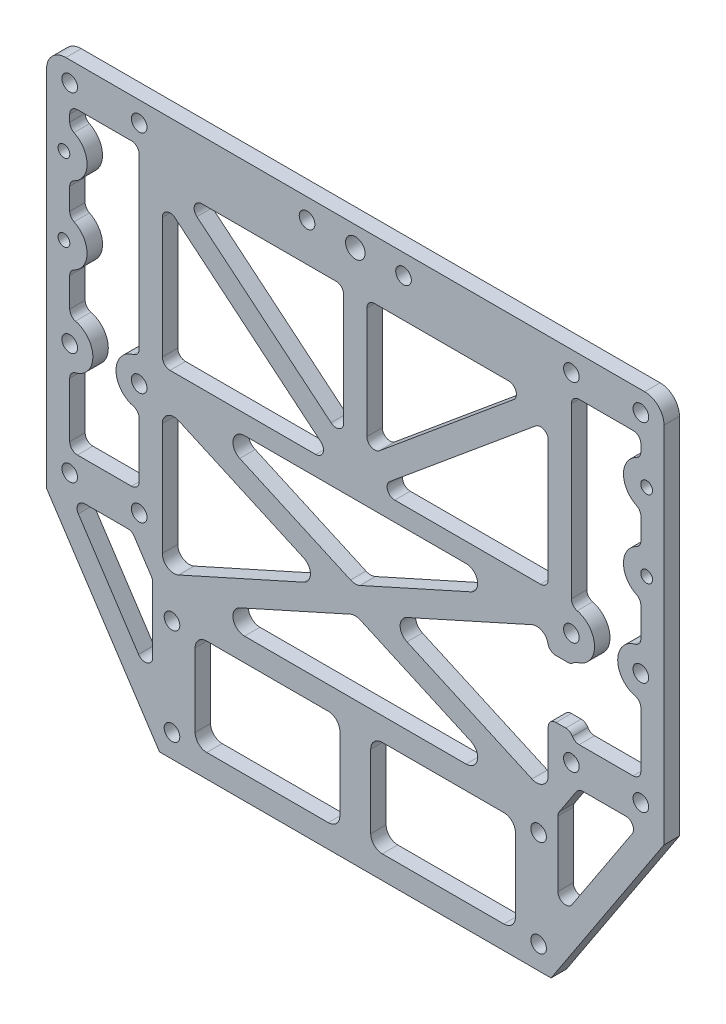
SolidWorks part; units mm, degrees
material "Thornel Mat VMA"
ref_plane "前视基准面" through (0, 0, 0) normal (0, 0, 1) x (1, 0, 0)
ref_plane "上视基准面" through (0, 0, 0) normal (0, 1, 0) x (1, 0, 0)
ref_plane "右视基准面" through (0, 0, 0) normal (1, 0, 0) x (0, 0, -1)
other "Configuration Table"
sketch "草图1" plane through (0, 0, 0) normal (0, 0, 1) x (1, 0, 0)
  line L0 (0, 0) -> (0, -50000) construction
  line L1 (-74, -14.5) -> (74, -14.5) construction
  line L2 (-74, -14.5) -> (-74, 14.5) construction
  line L3 (-74, 14.5) -> (74, 14.5) construction
  line L4 (74, -14.5) -> (74, 14.5) construction
  line L5 (-74, -14.5) -> (74, 14.5) construction
  line L6 (-74, 14.5) -> (74, -14.5) construction
  line L7 (-80, -14.5) -> (80, -14.5) construction
  line L8 (-80, -14.5) -> (-80, 14.5) construction
  line L9 (-80, 14.5) -> (80, 14.5) construction
  line L10 (80, -14.5) -> (80, 14.5) construction
  line L11 (-80, -14.5) -> (80, 14.5) construction
  line L12 (-80, 14.5) -> (80, -14.5) construction
  line L13 (-74, 14.5) -> (74, 14.5) construction
  line L14 (-74, 14.5) -> (-74, 73) construction
  line L15 (-74, 73) -> (74, 73) construction
  line L16 (74, 14.5) -> (74, 73) construction
  line L17 (-80, -14.5) -> (80, -14.5)
  line L18 (-80, -14.5) -> (-80, -21)
  line L19 (-80, -21) -> (80, -21)
  line L20 (80, -14.5) -> (80, -21)
  line L21 (-80, -21) -> (-50.7354, -65.5)
  line L22 (-47.5, -59.5) -> (47.5, -59.5) construction
  line L23 (-47.5, -59.5) -> (-47.5, -34.5) construction
  line L24 (-47.5, -34.5) -> (47.5, -34.5) construction
  line L25 (47.5, -59.5) -> (47.5, -34.5) construction
  line L26 (-47.5, -59.5) -> (47.5, -34.5) construction
  line L27 (-47.5, -34.5) -> (47.5, -59.5) construction
  line L28 (-50.7354, -65.5) -> (50.7354, -65.5)
  line L29 (50.7354, -65.5) -> (80, -21)
  line L31 (-80, -14.5) -> (80, -14.5)
  line L32 (-80, -14.5) -> (-80, 83)
  line L33 (-80, 83) -> (80, 83)
  line L34 (80, -14.5) -> (80, 83)
  circle A0 centre (-74, 14.5) radius 2.025
  circle A1 centre (-74, -14.5) radius 2.025
  circle A2 centre (74, -14.5) radius 2.025
  circle A3 centre (74, 14.5) radius 2.025
  circle A4 centre (-74, 73) radius 2.025
  circle A5 centre (74, 73) radius 2.025
  circle A6 centre (-47.5, -34.5) radius 2.025
  circle A7 centre (-47.5, -59.5) radius 2.025
  circle A8 centre (47.5, -34.5) radius 2.025
  circle A9 centre (47.5, -59.5) radius 2.025
  circle A10 centre (-47.5, -59.5) radius 6 construction
  circle A11 centre (74, 73) radius 6 construction
  point P0 (0, 0)
  point P6 (0, 0)
  point P22 (0, -47)
  dimension "D3" = 4.05
  dimension "D1" = 148
  dimension "D2" = 160
  dimension "D4" = 29
  dimension "D5" = 87.5
  dimension "D6" = 6.5
  dimension "D7" = 25
  dimension "D8" = 95
  dimension "D9" = 6
  dimension "D10" = 26
  dimension "D11" = 10
extrude "凸台-拉伸1" add sketch "草图1" along normal blind 4 contours A2 L17 L34 L33 L32 A1 A5 A4 A3 A0 | A2 L17 A1 L18 L19 L20 | L28 L29 L19 L21 A9 A8 A7 A6
sketch "草图2" plane through (0, 0, 4) normal (0, 0, 1) x (1, 0, 0)
  line L0 (0, 0) -> (0, -50000) construction
  circle A0 centre (-74, -14.5) radius 2.025 construction
  circle A1 centre (-74, 14.5) radius 2.025 construction
  circle A2 centre (-74, 73) radius 2.025 construction
  circle A3 centre (-74, -14.5) radius 2.025
  circle A4 centre (-74, 14.5) radius 2.025
  circle A5 centre (-74, 73) radius 2.025
  circle A6 centre (-56, 73) radius 2.025
  circle A7 centre (-56, 14.5) radius 2.025
  circle A8 centre (-56, -14.5) radius 2.025
  circle A9 centre (56, -14.5) radius 2.025
  circle A10 centre (56, 14.5) radius 2.025
  circle A11 centre (56, 73) radius 2.025
  dimension "D2" = 18
  dimension "D1" = 2
extrude "切除-拉伸1" cut sketch "草图2" against normal blind 10
sketch "草图3" plane through (0, 0, 4) normal (0, 0, 1) x (1, 0, 0)
  line L0 (-56, 73) -> (56, 73) construction
  circle A0 centre (0, 73) radius 2.525
  dimension "D1" = 5.05
extrude "切除-拉伸2" cut sketch "草图3" against normal blind 10
sketch "草图4" plane through (0, 0, 4) normal (0, 0, 1) x (1, 0, 0)
  line L0 (-80, -21) -> (-80, 83) construction
  line L1 (0, 0) -> (0, -50000) construction
  line L2 (-47.5, -34.5) -> (-47.5, -59.5) construction
  line L3 (-41.5, -59.5) -> (-4, -59.5)
  line L4 (-41.5, -59.5) -> (-41.5, -34.5)
  line L5 (-41.5, -34.5) -> (-4, -34.5)
  line L6 (-4, -59.5) -> (-4, -34.5)
  line L7 (-41.5, -59.5) -> (-4, -34.5) construction
  line L8 (-41.5, -34.5) -> (-4, -59.5) construction
  line L9 (4, -59.5) -> (41.5, -59.5)
  line L10 (4, -59.5) -> (4, -34.5)
  line L11 (4, -34.5) -> (41.5, -34.5)
  line L12 (41.5, -59.5) -> (41.5, -34.5)
  line L13 (4, -59.5) -> (41.5, -34.5) construction
  line L14 (4, -34.5) -> (41.5, -59.5) construction
  line L15 (-47.5, -47) -> (-50047.5, -47) construction
  line L16 (-50.7354, -65.5) -> (50.7354, -65.5) construction
  line L17 (-74.4629, -18.5) -> (-36.5763, -18.5) construction
  line L18 (-36.5763, -18.5) -> (-30, -28.5) construction
  line L19 (-30, -28.5) -> (-67.8866, -28.5) construction
  line L20 (-67.8866, -28.5) -> (-74.4629, -18.5) construction
  line L21 (-80, -21) -> (-50.7354, -65.5) construction
  line L22 (80, -21) -> (80, 83) construction
  line L23 (-80, 20.5) -> (80, 20.5) construction
  line L24 (-80, 20.5) -> (-80, -18.5) construction
  line L25 (-80, -18.5) -> (80, -18.5) construction
  line L26 (80, 20.5) -> (80, -18.5) construction
  line L27 (-48.7689, -31.2358) -> (51.2311, 13.7642)
  line L28 (-50, -28.5) -> (50, -28.5)
  line L29 (-50, -28.5) -> (-50, 16.5)
  line L30 (-50, 16.5) -> (50, 16.5)
  line L31 (50, -28.5) -> (50, 16.5)
  line L32 (-50, -28.5) -> (50, 16.5) construction
  line L33 (-50, 16.5) -> (50, -28.5) construction
  line L34 (-51.2311, 13.7642) -> (48.7689, -31.2358)
  line L35 (-51.2311, -25.7642) -> (48.7689, 19.2358)
  line L36 (-48.7689, 19.2358) -> (51.2311, -25.7642)
  circle A0 centre (-74, 14.5) radius 6
  circle A1 centre (-56, 14.5) radius 6
  circle A3 centre (-56, -14.5) radius 2.025 construction
  point P11 (-22.75, -47)
  point P16 (22.75, -47)
  point P27 (-47.5, -47)
  point P44 (0, -6)
  dimension "D1" = 8
  dimension "D2" = 6
  dimension "D3" = 6
  dimension "D4" = 6
  dimension "D5" = 4
  dimension "D6" = 6
  dimension "D7" = 30
  dimension "D8" = 4
  dimension "D9" = 3
  dimension "D10" = 3
extrude "切除-拉伸3" cut sketch "草图4" against normal blind 10 contours L30 L36 L35 | L29 L35 L34 | L27 L36 L31 | L34 L27 L28 | L9 L12 L11 L10 | L3 L6 L5 L4
fillet "圆角2" radius 3 20 edges at (42.6894, -28.5, 2) (-42.6894, -28.5, 2) (0, -9.2898, 2) (-50, 13.2102, 2) (-7.3106, -6, 2) (-50, -25.2102, 2) (-41.5, -34.5, 2) (-4, -34.5, 2) (-4, -59.5, 2) (-41.5, -59.5, 2) (42.6894, 16.5, 2) (0, -2.7102, 2) (-42.6894, 16.5, 2) (50, 13.2102, 2) (50, -25.2102, 2) (7.3106, -6, 2) (4, -34.5, 2) (41.5, -34.5, 2) (4, -59.5, 2) (41.5, -59.5, 2)
sketch "草图5" plane through (0, 0, 4) normal (0, 0, 1) x (1, 0, 0)
  line L0 (-73.8053, -19.5) -> (-57.8852, -19.5)
  line L1 (-57.8852, -19.5) -> (-52.5, -27.6887)
  line L2 (-52.5, -27.6887) -> (-52.5, -51.897)
  line L3 (-52.5, -51.897) -> (-73.8053, -19.5)
  line L4 (-80, -21) -> (-50.7354, -65.5) construction
  line L5 (-47.5, -34.5) -> (-47.5, -59.5) construction
  line L6 (0, 0) -> (0, -50000) construction
  line L8 (52.5, -27.6887) -> (52.5, -51.897)
  line L9 (57.8852, -19.5) -> (52.5, -27.6887)
  line L10 (73.8053, -19.5) -> (57.8852, -19.5)
  line L11 (52.5, -51.897) -> (73.8053, -19.5)
  circle A0 centre (-74, -14.5) radius 2.025 construction
  point P7 (-65.3677, -43.25)
  dimension "D3" = 5
  dimension "D1" = 6
  dimension "D2" = 5
  dimension "D4" = 6
extrude "切除-拉伸4" cut sketch "草图5" against normal blind 10
sketch "草图6" plane through (0, 0, 4) normal (0, 0, 1) x (1, 0, 0)
  line L0 (80, -21) -> (80, 83) construction
  line L1 (-80, -21) -> (-80, 83) construction
  line L2 (-74, 68) -> (-56, 68)
  line L3 (-74, 68) -> (-74, -9.5)
  line L4 (-74, -9.5) -> (-56, -9.5)
  line L5 (-56, 68) -> (-56, -9.5)
  line L6 (-28.7122, 16.5) -> (28.7122, 16.5) construction
  line L7 (0, 0) -> (0, -50000) construction
  line L8 (74, -9.5) -> (56, -9.5)
  line L9 (56, 68) -> (56, -9.5)
  line L10 (74, 68) -> (56, 68)
  line L11 (74, 68) -> (74, -9.5)
  line L17 (-50, 21.5) -> (50, 21.5)
  line L18 (-50, 21.5) -> (-50, 63)
  line L19 (-50, 63) -> (50, 63)
  line L20 (50, 21.5) -> (50, 63)
  line L21 (-50, 21.5) -> (50, 63) construction
  line L22 (-50, 63) -> (50, 21.5) construction
  circle A0 centre (-74, 14.5) radius 6
  circle A1 centre (-56, 14.5) radius 6
  circle A2 centre (56, 14.5) radius 6
  circle A3 centre (74, 14.5) radius 6
  circle A4 centre (-74, -14.5) radius 2.025 construction
  circle A5 centre (-74, 73) radius 2.025 construction
  circle A7 centre (0, 73) radius 2.525 construction
  point P31 (0, 42.25)
  dimension "D5" = 10
  dimension "D1" = 6
  dimension "D2" = 5
  dimension "D3" = 5
  dimension "D4" = 5
  dimension "D6" = 6
extrude "切除-拉伸5" cut sketch "草图6" against normal blind 10 contours L17 L20 L19 L18 | A1 L5 L2 L3 A0 L4 | A3 L11 L10 L9 A2 L8
sketch "草图7" plane through (0, 0, 4) normal (0, 0, 1) x (1, 0, 0)
  line L0 (-80, -21) -> (-80, 83) construction
  line L1 (-80, 78.2) -> (80, 78.2)
  line L2 (-80, 78.2) -> (-80, 83)
  line L3 (-80, 83) -> (80, 83)
  line L4 (80, 78.2) -> (80, 83)
  line L5 (80, -21) -> (80, 83) construction
  line L6 (-80, 83) -> (80, 83) construction
  dimension "D1" = 4.8
extrude "切除-拉伸7" cut sketch "草图7" against normal blind 10
fillet "圆角5" radius 5 2 edges at (80, 78.2, 2) (-80, 78.2, 2)
sketch "草图11" plane through (0, 0, 4) normal (0, 0, 1) x (1, 0, 0)
  line L0 (-50, 63) -> (0, 21.5) construction
  line L1 (-50, 21.5) -> (50, 21.5) construction
  line L2 (0, 21.5) -> (50, 63) construction
  line L3 (0, 21.5) -> (0, 63) construction
  line L4 (-50, 63) -> (50, 63) construction
  line L5 (-51.916, 60.6916) -> (-1.916, 19.1916)
  line L6 (1.916, 19.1916) -> (51.916, 60.6916)
  line L7 (3, 21.5) -> (3, 63)
  line L8 (-48.084, 65.3084) -> (1.916, 23.8084)
  line L9 (-1.916, 23.8084) -> (48.084, 65.3084)
  line L10 (-3, 21.5) -> (-3, 63)
  line L12 (-50, 63) -> (50, 63)
  line L13 (-50, 63) -> (-50, 21.5)
  line L14 (-50, 21.5) -> (50, 21.5)
  line L15 (50, 63) -> (50, 21.5)
  dimension "D1" = 3
  dimension "D2" = 3
extrude "凸台-拉伸2" add sketch "草图11" against normal up to surface (4 mm away) up to face at (-65, 21.875, 0)
fillet "圆角6" radius 2 36 edges at (74, 8.5, 2) (74, 20.5, 2) (74, -9.5, 2) (56, -9.5, 2) (56, 20.5, 2) (56, 8.5, 2) (56, 68, 2) (74, 68, 2) (73.8053, -19.5, 2) (52.5, -51.897, 2) (52.5, -27.6887, 2) (57.8852, -19.5, 2) (-57.8852, -19.5, 2) (-52.5, -27.6887, 2) (-52.5, -51.897, 2) (-73.8053, -19.5, 2) (50, 59.1013, 2) (50, 21.5, 2) (4.6973, 21.5, 2) (-56, 8.5, 2) (-56, 20.5, 2) (-56, -9.5, 2) (-74, 20.5, 2) (-74, 8.5, 2) (-74, 68, 2) (-56, 68, 2) (-3, 27.8887, 2) (-45.3027, 63, 2) (-3, 63, 2) (3, 27.8887, 2) (3, 63, 2) (45.3027, 63, 2) (-50, 21.5, 2) (-50, 59.1013, 2) (-4.6973, 21.5, 2) (-74, -9.5, 2)
sketch "草图13" plane through (0, 0, 4) normal (0, 0, 1) x (1, 0, 0)
  line L0 (-12.5, 73) -> (12.5, 73) construction
  circle A0 centre (-12.5, 73) radius 2.025
  circle A1 centre (12.5, 73) radius 2.025
  point P4 (0, 73)
  dimension "D1" = 4.05
  dimension "D2" = 25
extrude "切除-拉伸8" cut sketch "草图13" against normal blind 10
sketch "草图14" plane through (0, 0, 4) normal (0, 0, 1) x (1, 0, 0)
  line L0 (74, 14.5) -> (75.5, 14.5) construction
  line L1 (75.5, 14.5) -> (75.5, 37) construction
  line L2 (80, -21) -> (80, 73.2) construction
  line L3 (75.5, 37) -> (75.5, 57) construction
  line L4 (0, 0) -> (0, -50000) construction
  line L5 (-75.5, 37) -> (-75.5, 57) construction
  line L6 (-75.5, 14.5) -> (-75.5, 37) construction
  circle A0 centre (75.5, 37) radius 1.525
  circle A1 centre (75.5, 57) radius 1.525
  circle A2 centre (-75.5, 57) radius 1.525
  circle A3 centre (-75.5, 37) radius 1.525
  dimension "D1" = 4.5
  dimension "D3" = 3.05
  dimension "D2" = 22.5
  dimension "D4" = 20
extrude "切除-拉伸9" cut sketch "草图14" against normal blind 10
fillet "圆角7" radius 5 8 edges at (74, 56.725, 2) (74, 57.275, 2) (74, 36.725, 2) (74, 37.275, 2) (-74, 37.275, 2) (-74, 36.725, 2) (-74, 57.275, 2) (-74, 56.725, 2)
sketch "草图15" plane through (0, 0, 0) normal (0, 0, -1) x (-1, 0, 0)
  line L0 (-50, -20.5705) -> (-50, 8.5705) construction
  line L1 (-50, -7.5) -> (-57, -7.5)
  line L2 (-50, -7.5) -> (-50, 7.5)
  line L3 (-50, 7.5) -> (-57, 7.5)
  line L4 (-57, -7.5) -> (-57, 7.5)
  line L7 (-36.5, 7.5) -> (-77.5, 7.5) construction
  dimension "D1" = 15
  dimension "D2" = 7
extrude "切除-拉伸10" cut sketch "草图15" against normal blind 10
fillet "圆角8" radius 2 4 edges at (56, -7.5, 2) (56.1443, 7.5, 2) (50, -7.5, 2) (50, 7.5, 2)
sketch "草图16" plane through (0, 0, 0) normal (0, 0, -1) x (-1, 0, 0)
  line L0 (-74, 51.4931) -> (-74, 42.5069) construction
  line L1 (-74, 66) -> (-74, 62.5069) construction
  line L2 (-74, 51.4931) -> (-74, 42.5069)
  line L3 (-74, 66) -> (-74, 62.5069)
  line L4 (-74, 31.4931) -> (-74, 22.246) construction
  line L5 (-74, 31.4931) -> (-74, 22.246)
  line L6 (0, 0) -> (0, -50000) construction
  line L7 (74, 31.4931) -> (74, 22.246)
  line L8 (74, 51.4931) -> (74, 42.5069)
  line L9 (74, 66) -> (74, 62.5069)
  circle A0 centre (-75.5, 37) radius 6
  circle A1 centre (-75.5, 57) radius 6
  circle A2 centre (75.5, 57) radius 6
  circle A3 centre (75.5, 37) radius 6
  circle A4 centre (-75.5, 57) radius 1.525
  circle A5 centre (-75.5, 37) radius 1.525
  circle A6 centre (75.5, 57) radius 1.525
  circle A7 centre (75.5, 37) radius 1.525
  arc A8 (-72.5, 8.6905) -> (-72.5, 20.3095) centre (-74, 14.5) ccw construction
  arc A9 (-74, 51.4931) -> (-76.318, 55.713) centre (-79, 51.4931) ccw construction
  arc A10 (-76.318, 58.287) -> (-74, 62.5069) centre (-79, 62.5069) ccw construction
  arc A11 (-74, 51.4931) -> (-76.318, 55.713) centre (-79, 51.4931) ccw
  arc A12 (-76.318, 58.287) -> (-74, 62.5069) centre (-79, 62.5069) ccw
  arc A13 (-74, 31.4931) -> (-76.318, 35.713) centre (-79, 31.4931) ccw construction
  arc A14 (-76.318, 38.287) -> (-74, 42.5069) centre (-79, 42.5069) ccw construction
  arc A15 (-74, 31.4931) -> (-76.318, 35.713) centre (-79, 31.4931) ccw
  arc A16 (-76.318, 38.287) -> (-74, 42.5069) centre (-79, 42.5069) ccw
  arc A17 (74, 31.4931) -> (76.318, 35.713) centre (79, 31.4931) cw
  arc A18 (76.318, 38.287) -> (74, 42.5069) centre (79, 42.5069) cw
  arc A19 (74, 51.4931) -> (76.318, 55.713) centre (79, 51.4931) cw
  arc A20 (76.318, 58.287) -> (74, 62.5069) centre (79, 62.5069) cw
  dimension "D1" = 3.05
extrude "凸台-拉伸3" add sketch "草图16" against normal up to surface (4 mm away) contours A12 A4 A11 L2 A1 L3 | A16 A5 A15 L5 A0 L2 | A7 A18 L8 A3 L7 A17 | A6 A20 L9 A2 L8 A19
fillet "圆角9" radius 2 8 edges at (74, 31.1905, 2) (74, 42.8095, 2) (74, 51.1905, 2) (74, 62.8095, 2) (-74, 42.8095, 2) (-74, 31.1905, 2) (-74, 62.8095, 2) (-74, 51.1905, 2)
